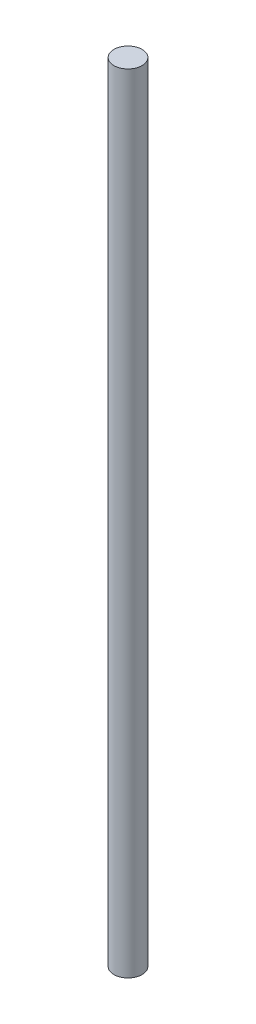
SolidWorks part; units mm, degrees
material "AISI 1020 Steel, Cold Rolled"
ref_plane "Front Plane" through (0, 0, 0) normal (0, 0, 1) x (1, 0, 0)
ref_plane "Top Plane" through (0, 0, 0) normal (0, 1, 0) x (1, 0, 0)
ref_plane "Right Plane" through (0, 0, 0) normal (1, 0, 0) x (0, 0, -1)
sketch "Sketch1" plane through (0, 0, 0) normal (0, 1, 0) x (1, 0, 0)
  circle A0 centre (0, 0) radius 3.175
  dimension "D1" = 6.35
extrude "Boss-Extrude1" add sketch "Sketch1" along normal mid plane 177.8
